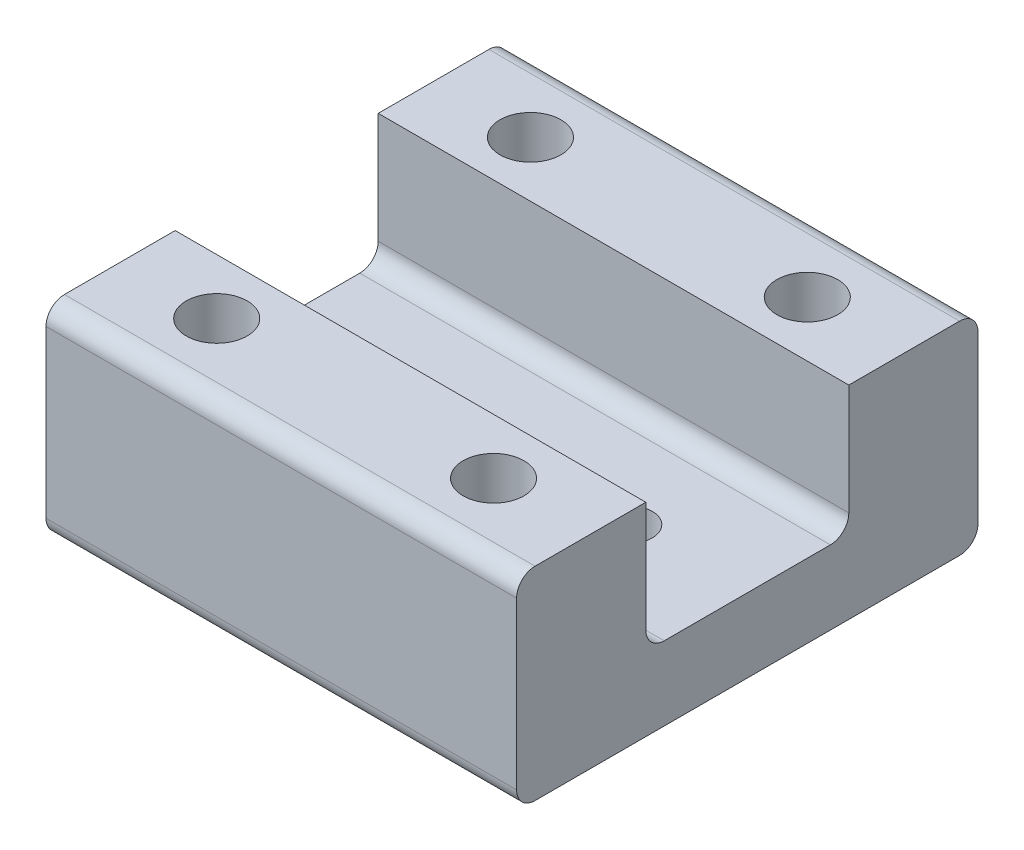
SolidWorks part; units mm, degrees
material "6063-T5"
ref_plane "前视基准面" through (0, 0, 0) normal (0, 0, 1) x (1, 0, 0)
ref_plane "上视基准面" through (0, 0, 0) normal (0, 1, 0) x (1, 0, 0)
ref_plane "右视基准面" through (0, 0, 0) normal (1, 0, 0) x (0, 0, -1)
other "Configuration Table"
sketch "草图1" plane through (0, 0, 0) normal (0, 1, 0) x (1, 0, 0)
  line L1 (-12.75, -12.5) -> (12.75, -12.5)
  line L2 (-12.75, -12.5) -> (-12.75, 12.5)
  line L3 (-12.75, 12.5) -> (12.75, 12.5)
  line L4 (12.75, -12.5) -> (12.75, 12.5)
  line L5 (-12.75, -12.5) -> (12.75, 12.5) construction
  line L6 (-12.75, 12.5) -> (12.75, -12.5) construction
  point P0 (0, 0)
  dimension "D1" = 25.5
  dimension "D2" = 25
extrude "凸台-拉伸1" add sketch "草图1" along normal blind 4
sketch "草图2" plane through (0, 0, 0) normal (0, -1, 0) x (1, 0, 0)
  line L1 (-7.5, 7.5) -> (7.5, 7.5) construction
  line L2 (-7.5, 7.5) -> (-7.5, -7.5) construction
  line L3 (-7.5, -7.5) -> (7.5, -7.5) construction
  line L4 (7.5, 7.5) -> (7.5, -7.5) construction
  line L5 (-7.5, 7.5) -> (7.5, -7.5) construction
  line L6 (-7.5, -7.5) -> (7.5, 7.5) construction
  point P0 (0, 0)
  dimension "D1" = 15
sketch "草图5" plane through (0, 0, 0) normal (0, -1, 0) x (1, 0, 0)
  line L0 (0, 0) -> (50000, 0) construction
  line L1 (12.75, 12.5) -> (12.75, -12.5) construction
  circle A0 centre (6.35, 0) radius 1.525
  circle A1 centre (-6.35, 0) radius 1.525
  dimension "D2" = 3.05
  dimension "D3" = 6.4
  dimension "D1" = 12.7
sketch "草图6" plane through (0, 4, 0) normal (0, 1, 0) x (1, 0, 0)
  line L0 (-12.75, 12.5) -> (-12.75, -12.5) construction
  line L1 (12.75, 12.5) -> (-12.75, 12.5)
  line L2 (12.75, 12.5) -> (12.75, 5.5)
  line L3 (12.75, 5.5) -> (-12.75, 5.5)
  line L4 (-12.75, 12.5) -> (-12.75, 5.5)
  line L5 (0, 0) -> (12.75, 0) construction
  line L6 (12.75, -12.5) -> (-12.75, -12.5)
  line L7 (12.75, -12.5) -> (12.75, -5.5)
  line L8 (12.75, -5.5) -> (-12.75, -5.5)
  line L9 (-12.75, -12.5) -> (-12.75, -5.5)
  line L10 (12.75, -12.5) -> (12.75, 12.5) construction
  dimension "D1" = 7
extrude "凸台-拉伸2" add sketch "草图6" along normal blind 7
sketch "草图7" plane through (0, 0, 0) normal (0, -1, 0) x (1, 0, 0)
  line L0 (-12.75, -12.5) -> (-12.75, 12.5) construction
  line L1 (-7.5, 8.5) -> (7.5, 8.5) construction
  line L2 (-7.5, 8.5) -> (-7.5, -8.5) construction
  line L3 (-7.5, -8.5) -> (7.5, -8.5) construction
  line L4 (7.5, 8.5) -> (7.5, -8.5) construction
  circle A0 centre (7.5, -8.5) radius 2.025
  circle A1 centre (-7.5, 8.5) radius 2.025
  circle A2 centre (7.5, 8.5) radius 2.025
  circle A3 centre (-7.5, -8.5) radius 2.025
  dimension "D1" = 4.05
  dimension "D2" = 15
  dimension "D3" = 8.5
  dimension "D4" = 5.25
  dimension "D5" = 8.5
hole_wizard "M3 螺纹孔1" positions "3D草图3" profile "草图10" tap size "M3" standard "GB" end condition through all
sketch3d "3D草图3"
  point P0 (6.35, 0, 0)
  point P3 (-6.35, 0, 0)
sketch "草图10" plane through (6.35, 0, 0) normal (1, 0, 0) x (0, 0, -1)
  line L0 (0, 0) -> (0, 11)
  line L1 (0, 11) -> (1.25, 11)
  line L2 (1.25, 11) -> (1.25, 0)
  line L5 (1.25, 0) -> (0, 0)
  line L11 (0, -6.35) -> (0, 107.95) construction
  dimension "通孔螺纹孔钻头直径" = 2.5
  dimension "通孔螺纹孔钻头深度" = 11
cosmetic thread "孔螺蚊线5" parameters "D2"=3
cosmetic thread "孔螺蚊线6" parameters "D2"=3
hole_wizard "M4 螺纹孔3" positions "3D草图6" profile "草图12" tap size "M4" standard "GB" end condition through all
sketch3d "3D草图6"
  point P0 (7.5, 0, 8.5)
  point P3 (-7.5, 0, 8.5)
  point P6 (-7.5, 0, -8.5)
  point P9 (7.5, 0, -8.5)
cosmetic thread "孔螺蚊线7" parameters "D2"=4
cosmetic thread "孔螺蚊线8" parameters "D2"=4
cosmetic thread "孔螺蚊线9" parameters "D2"=4
cosmetic thread "孔螺蚊线10" parameters "D2"=4
sketch "草图12" plane through (7.5, 0, 8.5) normal (1, 0, 0) x (0, 0, -1)
  line L0 (0, 0) -> (0, 11)
  line L1 (0, 11) -> (1.65, 11)
  line L2 (1.65, 11) -> (1.65, 0)
  line L5 (1.65, 0) -> (0, 0)
  line L11 (0, -6.35) -> (0, 107.95) construction
  dimension "通孔螺纹孔钻头直径" = 3.3
  dimension "通孔螺纹孔钻头深度" = 11
fillet "圆角1" radius 1 6 edges at (0, 0, -12.5) (0, 11, -12.5) (0, 4, -5.5) (0, 4, 5.5) (0, 11, 12.5) (0, 0, 12.5)
